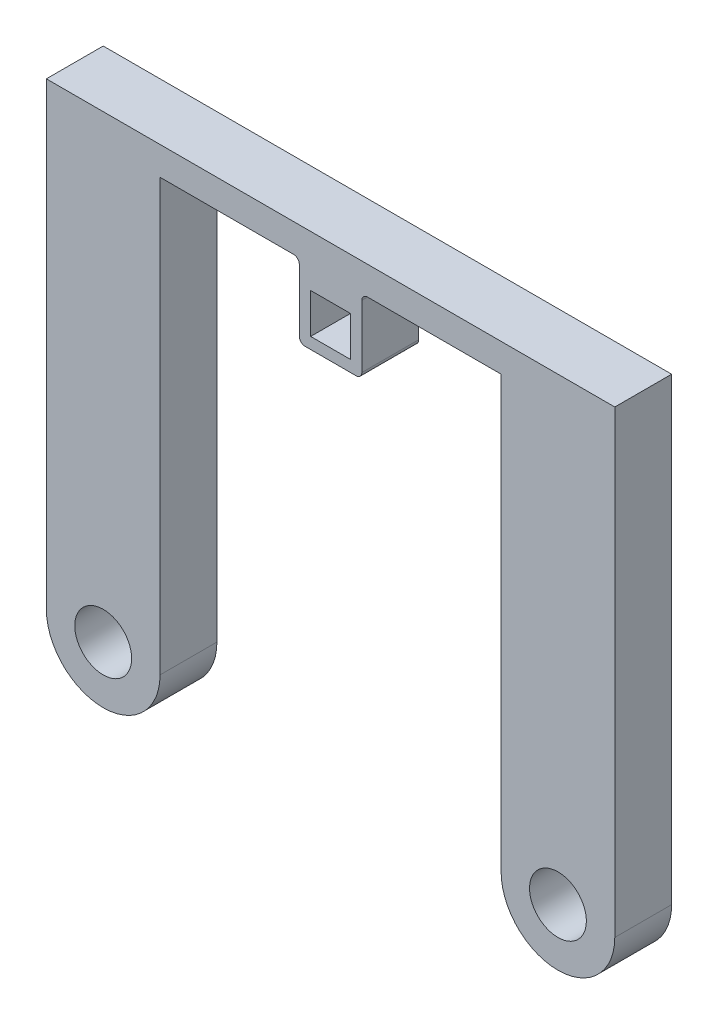
SolidWorks part; units mm, degrees
ref_plane "Front Plane" through (0, 0, 0) normal (0, 0, 1) x (1, 0, 0)
ref_plane "Top Plane" through (0, 0, 0) normal (0, 1, 0) x (1, 0, 0)
ref_plane "Right Plane" through (0, 0, 0) normal (1, 0, 0) x (0, 0, -1)
sketch "Sketch1" plane through (0, 0, 0) normal (0, 0, 1) x (1, 0, 0)
  line L0 (0, -49.9495) -> (0, 49.9495) construction
  line L1 (-50, 0) -> (-50, 80.8172)
  line L2 (-50, 80.8172) -> (-30, 80.8172)
  line L3 (-30, 80.8172) -> (-30, 0)
  line L4 (30, 0) -> (30, 80.8172)
  line L5 (30, 80.8172) -> (50, 80.8172)
  line L6 (50, 80.8172) -> (50, 0)
  line L7 (-30, 75.8172) -> (30, 75.8172)
  line L8 (-30, 80.8172) -> (30, 80.8172)
  circle A0 centre (-40, 0) radius 10
  circle A1 centre (40, 0) radius 10
  circle A2 centre (-40, 0) radius 5
  circle A3 centre (40, 0) radius 5
  dimension "D2" = 20
  dimension "D3" = 10
  dimension "D1" = 80
  dimension "D4" = 5
extrude "Boss-Extrude1" add sketch "Sketch1" along normal mid plane 10 contours A0 L3 L2 L1 | L8 L3 L7 L4 | L4 A1 L6 L5 | A0 A2 | A1 A3
sketch "Sketch2" plane through (0, 0, 5) normal (0, 0, 1) x (1, 0, 0)
  line L0 (-30, 75.8172) -> (30, 75.8172) construction
  line L2 (-5.5, 62.8172) -> (5.5, 62.8172)
  line L3 (-5.5, 62.8172) -> (-5.5, 75.8172)
  line L4 (-5.5, 75.8172) -> (5.5, 75.8172)
  line L5 (5.5, 62.8172) -> (5.5, 75.8172)
  line L6 (-5.5, 62.8172) -> (5.5, 75.8172) construction
  line L7 (-5.5, 75.8172) -> (5.5, 62.8172) construction
  line L8 (0, 69.3172) -> (0, 0) construction
  line L9 (-3.5, 71.8172) -> (3.5, 71.8172)
  line L10 (-3.5, 71.8172) -> (-3.5, 64.8172)
  line L11 (-3.5, 64.8172) -> (3.5, 64.8172)
  line L12 (3.5, 71.8172) -> (3.5, 64.8172)
  line L13 (-3.5, 71.8172) -> (3.5, 64.8172) construction
  line L14 (-3.5, 64.8172) -> (3.5, 71.8172) construction
  point P0 (0, 69.3172)
  point P7 (0, 68.3172)
  point P12 (0, 0)
  point P13 (0, 68.3172)
  dimension "D1" = 7
  dimension "D2" = 7
  dimension "D3" = 7.5
  dimension "D4" = 2
  dimension "D5" = 2
extrude "Boss-Extrude2" add sketch "Sketch2" against normal up to surface (10 mm away)
fillet "Fillet1" radius 1 4 edges at (-5.5, 75.8172, 0) (5.5, 75.8172, 0) (5.5, 62.8172, 0) (-5.5, 62.8172, 0)
